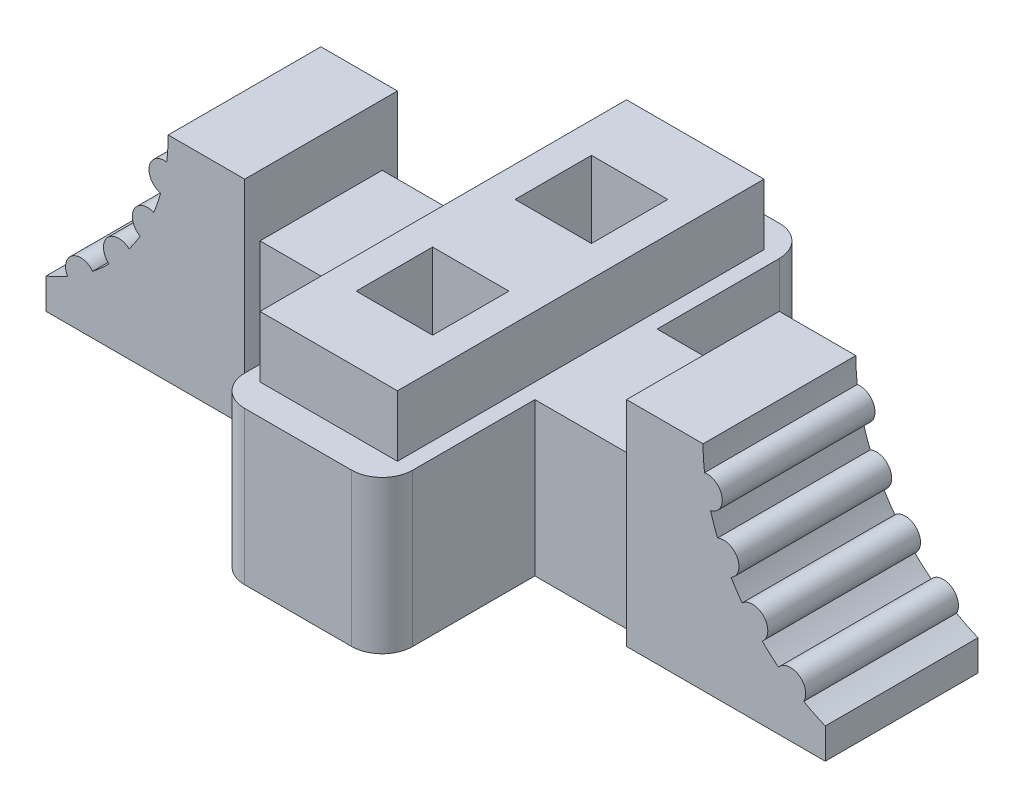
SolidWorks part; units mm, degrees
ref_plane "Front Plane" through (0, 0, 0) normal (0, 0, 1) x (1, 0, 0)
ref_plane "Top Plane" through (0, 0, 0) normal (0, 1, 0) x (1, 0, 0)
ref_plane "Right Plane" through (0, 0, 0) normal (1, 0, 0) x (0, 0, -1)
sketch "Sketch1" plane through (0, 0, 0) normal (0, 1, 0) x (1, 0, 0)
  line L1 (0, 0) -> (11, 0)
  line L2 (0, 0) -> (0, 28)
  line L3 (0, 28) -> (11, 28)
  line L4 (11, 0) -> (11, 28)
extrude "Boss-Extrude1" add sketch "Sketch1" along normal blind 10
sketch "Sketch2" plane through (0, 0, 0) normal (0, -1, 0) x (1, 0, 0)
  line L0 (0, -14) -> (11, -14) construction
  line L1 (0, -28) -> (0, 0) construction
  line L2 (11, 0) -> (11, -28) construction
  line L3 (5.5, -14) -> (5.5, -6) construction
  circle A0 centre (5.5, -6) radius 3
  circle A1 centre (5.5, -22) radius 3
extrude "Cut-Extrude1" cut sketch "Sketch2" against normal blind 5
sketch "Sketch3" plane through (0, 10, 0) normal (0, 1, 0) x (1, 0, 0)
  line L0 (0, 14) -> (11, 14) construction
  line L1 (0, 28) -> (0, 0) construction
  line L2 (11, 0) -> (11, 28) construction
  line L3 (5.5, 14) -> (5.5, 19.2) construction
  line L4 (3, 11.3) -> (8, 11.3)
  line L5 (3, 16.7) -> (8, 16.7)
  line L6 (3, 16.7) -> (3, 21.7)
  line L7 (3, 21.7) -> (8, 21.7)
  line L8 (8, 16.7) -> (8, 21.7)
  line L9 (3, 16.7) -> (8, 21.7) construction
  line L10 (3, 21.7) -> (8, 16.7) construction
  line L11 (3, 11.3) -> (3, 6.3)
  line L12 (3, 6.3) -> (8, 6.3)
  line L13 (8, 11.3) -> (8, 6.3)
extrude "Cut-Extrude2" cut sketch "Sketch3" against normal blind 1
fillet "Fillet1" radius 2 4 edges at (0, 5, 0) (11, 5, 0) (0, 5, -28) (11, 5, -28)
sketch "Sketch4" plane through (0, 10, 0) normal (0, 1, 0) x (1, 0, 0)
  line L0 (-7, 10) -> (3, 10)
  line L1 (-7, 10) -> (-7, 18)
  line L2 (18, 10) -> (18, 18)
  line L3 (-7, 18) -> (3, 18)
  line L4 (-7, 10) -> (18, 18) construction
  line L5 (18, 10) -> (-7, 18) construction
  line L6 (3, 16.7) -> (3, 18)
  line L7 (3, 21.7) -> (3, 16.7) construction
  line L8 (3, 16.7) -> (8, 16.7)
  line L9 (8, 16.7) -> (8, 18)
  line L10 (8, 16.7) -> (8, 21.7) construction
  line L11 (8, 18) -> (18, 18)
  line L12 (5.5, 14) -> (11, 14) construction
  line L13 (11, 2) -> (11, 26) construction
  line L14 (8, 11.3) -> (8, 10)
  line L15 (3, 11.3) -> (8, 11.3)
  line L16 (3, 11.3) -> (3, 10)
  line L17 (8, 10) -> (18, 10)
  point P1 (5.5, 14)
extrude "Boss-Extrude2" add sketch "Sketch4" against normal up to surface (10 mm away) up to face at (5.5, 0, -19)
ref_plane "Plane1" through (0, 0, -14) normal (0, 0, -1) x (-1, 0, 0)
sketch "Sketch5" plane through (0, 0, -14) normal (0, 0, -1) x (-1, 0, 0)
  line L0 (-18, 10) -> (-18, 14)
  line L1 (-18, 14) -> (-23.0096, 14)
  line L2 (-18, 0) -> (-31.0096, 0)
  line L3 (-31.0096, 0) -> (-31.0096, 2)
  line L4 (-36.0096, 14) -> (-24.2478, 11.6212) construction
  line L5 (-36.0096, 14) -> (-25.2566, 8.6543) construction
  line L6 (-18, 10) -> (-18, 0)
  arc A0 (-23.0096, 14) -> (-23.1072, 12.4101) centre (-36.0096, 14) cw
  arc A1 (-23.1072, 12.4101) -> (-23.5034, 10.4512) centre (-23.2676, 11.423) ccw
  arc A2 (-23.9562, 9.1303) -> (-24.8446, 7.341) centre (-24.3584, 8.2148) ccw
  arc A3 (-25.5681, 6.2556) -> (-26.8789, 4.7464) centre (-26.2471, 5.5215) ccw
  arc A4 (-27.9484, 3.8011) -> (-29.6026, 2.6885) centre (-28.7305, 3.178) ccw
  arc A5 (-26.8789, 4.7464) -> (-27.9484, 3.8011) centre (-36.0096, 14) cw
  arc A6 (-24.8446, 7.341) -> (-25.5681, 6.2556) centre (-36.0096, 14) cw
  arc A7 (-23.5034, 10.4512) -> (-23.9562, 9.1303) centre (-36.0096, 14) cw
  arc A8 (-29.6026, 2.6885) -> (-31.0096, 2) centre (-36.0096, 14) cw
  point P12 (-23.2676, 11.423)
  point P14 (-24.3688, 8.2129)
  point P15 (-26.2632, 5.3972)
  point P16 (-28.8219, 3.1678)
  dimension "D1" = 4
  dimension "D2" = 15
extrude "Boss-Extrude3" add sketch "Sketch5" along normal blind 5 and the other way blind 5
ref_plane "Plane2" through (5.5, 0, 0) normal (-1, 0, 0) x (0, 0, 1)
mirror "Mirror1" about plane through (5.5, 0, 0) normal (-1, 0, 0) of "Boss-Extrude3"
sketch "Sketch6" plane through (0, 10, 0) normal (0, 1, 0) x (1, 0, 0)
  line L0 (5.5, 16.7) -> (5.5, 11.3) construction
  line L1 (3, 16.7) -> (8, 16.7) construction
  line L2 (8, 11.3) -> (3, 11.3) construction
  line L3 (1, 2) -> (1, 26)
  line L4 (1, 2) -> (10, 2)
  line L5 (1, 26) -> (10, 26)
  line L6 (10, 2) -> (10, 26)
  line L7 (1, 2) -> (10, 26) construction
  line L8 (1, 26) -> (10, 2) construction
  line L10 (3, 16.7) -> (8, 16.7)
  line L11 (3, 16.7) -> (3, 21.7)
  line L12 (3, 21.7) -> (8, 21.7)
  line L13 (8, 16.7) -> (8, 21.7)
  line L14 (3, 6.3) -> (8, 6.3)
  line L15 (3, 6.3) -> (3, 11.3)
  line L16 (3, 11.3) -> (8, 11.3)
  line L17 (8, 6.3) -> (8, 11.3)
  point P7 (5.5, 14)
extrude "Boss-Extrude4" add sketch "Sketch6" along normal blind 4
